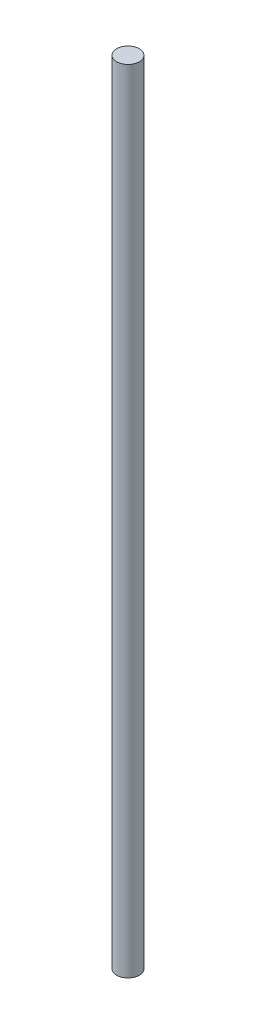
SolidWorks part; units mm, degrees
ref_plane "Plan de face" through (0, 0, 0) normal (0, 0, 1) x (1, 0, 0)
ref_plane "Plan de dessus" through (0, 0, 0) normal (0, 1, 0) x (1, 0, 0)
ref_plane "Plan de droite" through (0, 0, 0) normal (1, 0, 0) x (0, 0, -1)
sketch "Esquisse1" plane through (0, 0, 0) normal (0, 1, 0) x (1, 0, 0)
  circle A0 centre (0, 0) radius 3
  dimension "D1" = 6
extrude "Boss.-Extru.1" add sketch "Esquisse1" along normal blind 210
